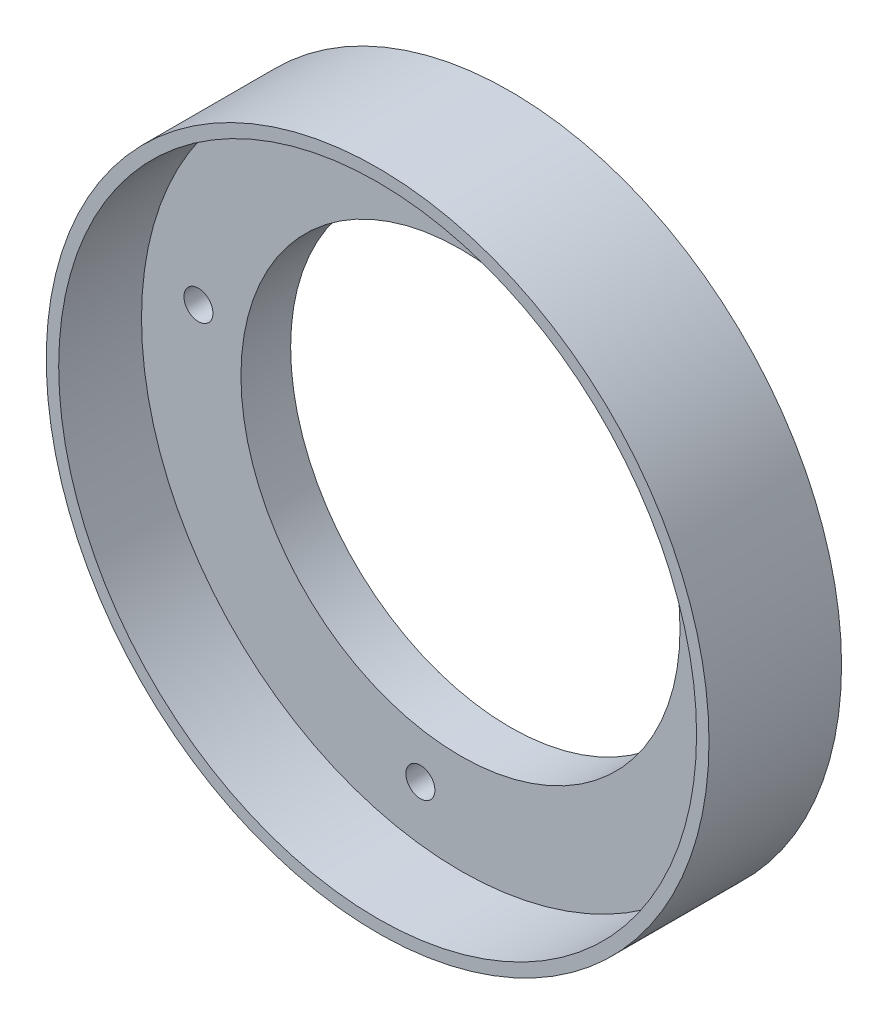
SolidWorks part; units mm, degrees
ref_plane "Płaszczyzna przednia" through (0, 0, 0) normal (0, 0, 1) x (1, 0, 0)
ref_plane "Płaszczyzna górna" through (0, 0, 0) normal (0, 1, 0) x (1, 0, 0)
ref_plane "Płaszczyzna prawa" through (0, 0, 0) normal (1, 0, 0) x (0, 0, -1)
sketch "Sketch1" plane through (0, 0, 0) normal (0, 0, 1) x (1, 0, 0)
  circle A0 centre (0, 0) radius 26.5
  circle A1 centre (0, 0) radius 40
  dimension "D1" = 53
  dimension "D2" = 80
extrude "Boss-Extrude1" add sketch "Sketch1" along normal blind 6
sketch "Sketch2" plane through (0, 0, 6) normal (0, 0, 1) x (1, 0, 0)
  line L0 (-6.0493, -39.5399) -> (6.0493, 39.5399) construction
  line L1 (39.5399, -6.0493) -> (-39.5399, 6.0493) construction
  circle A0 centre (0, 0) radius 40 construction
  circle A1 centre (-31.6319, 4.8394) radius 1.75
  circle A2 centre (4.8394, 31.6319) radius 1.75
  circle A3 centre (31.6319, -4.8394) radius 1.75
  circle A4 centre (-4.8394, -31.6319) radius 1.75
  point P8 (0, 0)
  point P12 (0, 0)
  dimension "D2" = 64
  dimension "D3" = 64
  dimension "D4" = 32
  dimension "D5" = 32
  dimension "D6" = 32
  dimension "D7" = 32
  dimension "D8" = 3.5
  dimension "D9" = 3.5
  dimension "D10" = 3.5
  dimension "D11" = 3.5
  dimension "D1" = 90
extrude "Cut-Extrude1" cut sketch "Sketch2" against normal through all
sketch "Sketch3" plane through (0, 0, 6) normal (0, 0, 1) x (1, 0, 0)
  circle A0 centre (0, 0) radius 38.5
  circle A2 centre (0, 0) radius 40
  dimension "D1" = 77
extrude "Boss-Extrude2" add sketch "Sketch3" along normal blind 10
